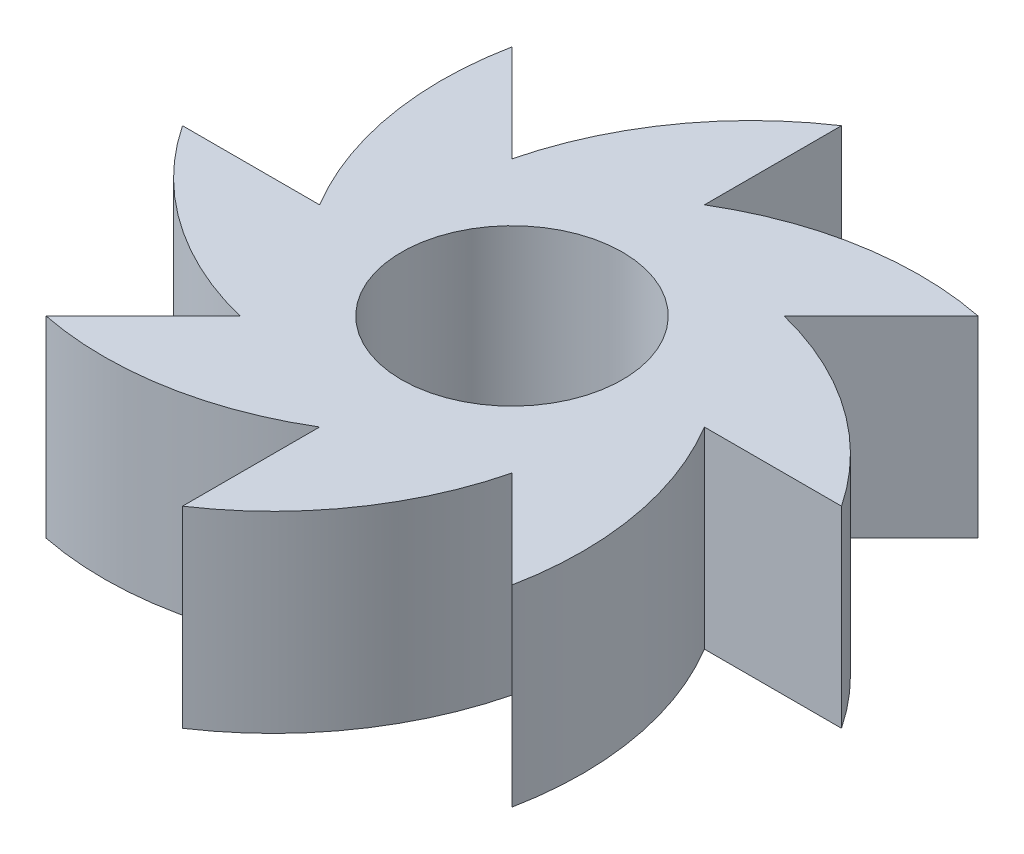
SolidWorks part; units mm, degrees
ref_plane "Спереди" through (0, 0, 0) normal (0, 0, 1) x (1, 0, 0)
ref_plane "Сверху" through (0, 0, 0) normal (0, 1, 0) x (1, 0, 0)
ref_plane "Справа" through (0, 0, 0) normal (1, 0, 0) x (0, 0, -1)
other "Configuration Table"
sketch "Эскиз1" plane through (0, 0, 0) normal (0, 1, 0) x (1, 0, 0)
  line L0 (0, 0) -> (0, 80.5) construction
  line L1 (0, 0) -> (80.5, 0) construction
  line L2 (0, 0) -> (56.9221, 56.9221) construction
  line L3 (56.9221, 56.9221) -> (33.234, 33.234)
  line L4 (80.5, 0) -> (47, 0)
  line L5 (56.9221, -56.9221) -> (33.234, -33.234)
  line L6 (0, -80.5) -> (0, -47)
  line L7 (-56.9221, -56.9221) -> (-33.234, -33.234)
  line L8 (-80.5, 0) -> (-47, 0)
  line L9 (-56.9221, 56.9221) -> (-33.234, 33.234)
  line L10 (0, 80.5) -> (0, 47)
  circle A0 centre (0, 0) radius 80.5 construction
  arc A1 (47, 0) -> (0, 47) centre (0, 0) ccw
  circle A2 centre (0, 0) radius 27
  arc A3 (0, 47) -> (56.9221, 56.9221) centre (41.2716, -21.5321) cw
  arc A4 (0, -47) -> (47, 0) centre (0, 0) ccw
  arc A5 (-47, 0) -> (0, -47) centre (0, 0) ccw
  arc A6 (0, 47) -> (-47, 0) centre (0, 0) ccw
  arc A7 (33.234, 33.234) -> (80.5, 0) centre (13.958, -44.409) cw
  arc A8 (47, 0) -> (56.9221, -56.9221) centre (-21.5321, -41.2716) cw
  arc A9 (33.234, -33.234) -> (0, -80.5) centre (-44.409, -13.958) cw
  arc A10 (0, -47) -> (-56.9221, -56.9221) centre (-41.2716, 21.5321) cw
  arc A11 (-33.234, -33.234) -> (-80.5, 0) centre (-13.958, 44.409) cw
  arc A12 (-47, 0) -> (-56.9221, 56.9221) centre (21.5321, 41.2716) cw
  arc A13 (-33.234, 33.234) -> (0, 80.5) centre (44.409, 13.958) cw
  point P20 (0, 0)
  point P45 (0, 0)
  dimension "D1" = 161
  dimension "D2" = 94
  dimension "D3" = 54
  dimension "D5" = 80
  dimension "D4" = 56.9221
  dimension "D6" = 4
  dimension "D7" = 8
extrude "Бобышка-Вытянуть1" add sketch "Эскиз1" along normal blind 47 contours A1 A6 A5 A4 A2 | A12 A6 L9 | A13 A6 L10 | A3 A1 L3 | A7 A1 L4 | A8 A4 L5 | A9 A4 L6 | A10 A5 L7 | A11 A5 L8
